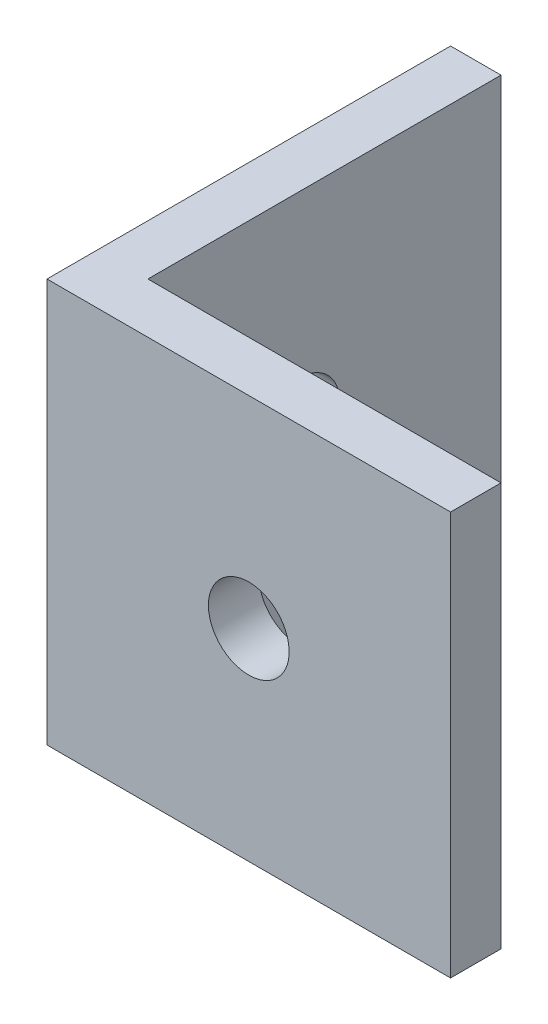
SolidWorks part; units mm, degrees
ref_plane "Front Plane" through (0, 0, 0) normal (0, 0, 1) x (1, 0, 0)
ref_plane "Top Plane" through (0, 0, 0) normal (0, 1, 0) x (1, 0, 0)
ref_plane "Right Plane" through (0, 0, 0) normal (1, 0, 0) x (0, 0, -1)
sketch "Sketch1" plane through (0, 0, 0) normal (0, 1, 0) x (1, 0, 0)
  line L1 (0, 0) -> (3.175, 0)
  line L2 (0, 0) -> (0, 25.4)
  line L3 (0, 25.4) -> (3.175, 25.4)
  line L4 (3.175, 3.175) -> (3.175, 25.4)
  line L5 (0, 0) -> (3.175, 25.4) construction
  line L6 (0, 25.4) -> (3.175, 0) construction
  line L7 (3.175, 0) -> (25.4, 0)
  line L9 (3.175, 3.175) -> (25.4, 3.175)
  line L10 (25.4, 0) -> (25.4, 3.175)
  line L11 (3.175, 0) -> (25.4, 3.175) construction
  line L12 (3.175, 3.175) -> (25.4, 0) construction
  point P4 (1.5875, 12.7)
  point P9 (14.2875, 1.5875)
  dimension "D1" = 25.4
  dimension "D2" = 25.4
  dimension "D3" = 3.175
  dimension "D4" = 3.175
extrude "Boss-Extrude1" add sketch "Sketch1" along normal blind 25.4
sketch "Sketch2" plane through (3.175, 0, 0) normal (1, 0, 0) x (0, 0, -1)
  line L0 (3.175, 25.4) -> (25.4, 25.4) construction
  line L1 (25.4, 25.4) -> (25.4, 0) construction
  circle A0 centre (12.7, 12.7) radius 2.54
  dimension "D1" = 5.08
  dimension "D2" = 12.7
  dimension "D3" = 12.7
extrude "Cut-Extrude1" cut sketch "Sketch2" against normal blind 25.4
sketch "Sketch3" plane through (0, 0, -3.175) normal (0, 0, -1) x (-1, 0, 0)
  line L0 (-25.4, 25.4) -> (-25.4, 0) construction
  line L1 (-25.4, 25.4) -> (-3.175, 25.4) construction
  circle A0 centre (-12.7, 12.7) radius 2.54
  dimension "D1" = 5.08
  dimension "D2" = 12.7
  dimension "D3" = 12.7
extrude "Cut-Extrude2" cut sketch "Sketch3" against normal blind 25.4
